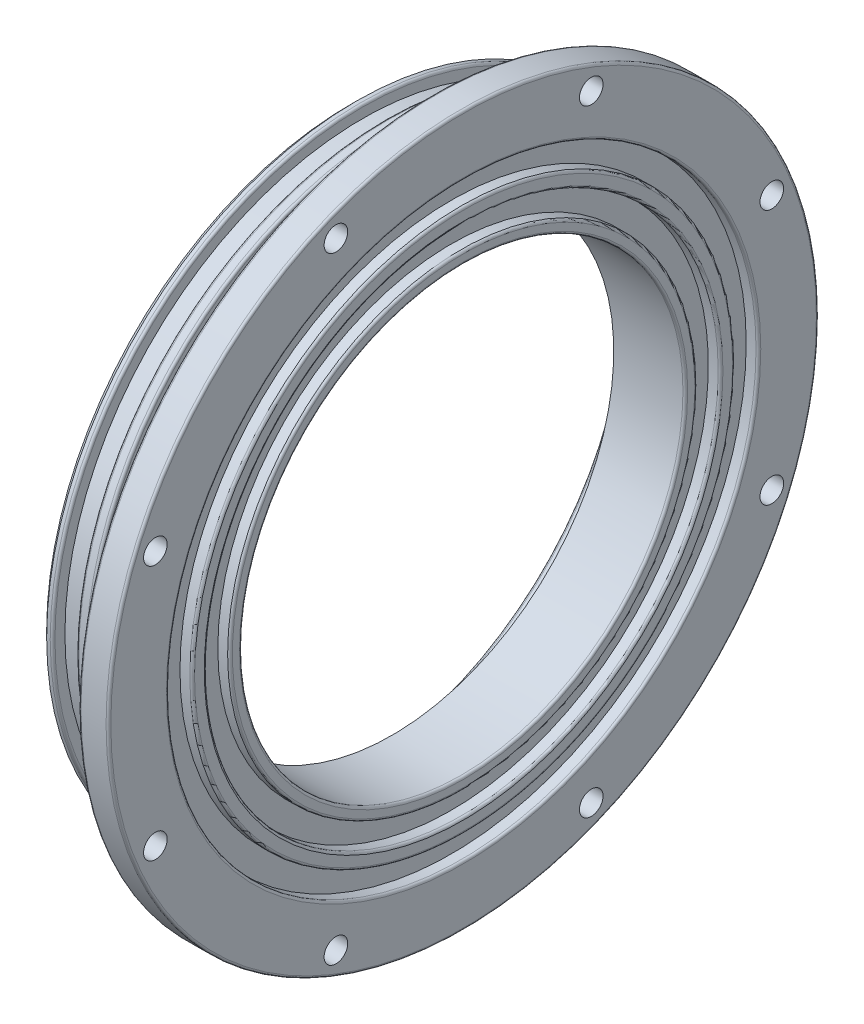
SolidWorks part; units mm, degrees
ref_plane "Front Plane" through (0, 0, 0) normal (0, 0, 1) x (1, 0, 0)
ref_plane "Top Plane" through (0, 0, 0) normal (0, 1, 0) x (1, 0, 0)
ref_plane "Right Plane" through (0, 0, 0) normal (1, 0, 0) x (0, 0, -1)
sketch "Sketch1" plane through (0, 0, 0) normal (0, 0, 1) x (1, 0, 0)
  line L0 (0, 0) -> (0, -58.42) construction
  line L5 (24.1999, -76) -> (17.8298, -76)
  line L6 (17.8298, -76) -> (17.8298, -66.421)
  line L7 (17.8298, -66.421) -> (0, -66.421) construction
  line L8 (0, -66.294) -> (0, -58.42)
  line L9 (0, -58.42) -> (8.89, -58.42)
  line L10 (0, -66.294) -> (2.54, -66.294)
  line L11 (2.54, -66.294) -> (2.54, -63.6575)
  line L12 (2.54, -63.6575) -> (7.6449, -63.6575)
  line L13 (7.6449, -63.6575) -> (7.6449, -66.294)
  line L14 (7.6449, -66.294) -> (10.1849, -66.294)
  line L15 (10.1849, -66.294) -> (10.1849, -63.6575)
  line L16 (10.1849, -63.6575) -> (15.2898, -63.6575)
  line L17 (15.2898, -63.6575) -> (15.2898, -66.294)
  line L18 (15.2898, -66.294) -> (17.8298, -66.294)
  line L19 (17.8298, -66.294) -> (17.8298, -66.421)
  line L20 (0, -66.421) -> (0, -66.294) construction
  line L24 (0, 0) -> (6.2477, 0) construction
  line L25 (8.89, -58.42) -> (8.89, -47.4495)
  line L26 (8.89, -47.4495) -> (24.1999, -47.4495)
  line L27 (24.1999, -47.4495) -> (24.1999, -49.9895)
  line L28 (24.1999, -49.9895) -> (21.59, -49.9895)
  line L29 (21.59, -49.9895) -> (21.59, -54.9896)
  line L30 (21.59, -54.9896) -> (24.1999, -54.9896)
  line L31 (24.1999, -54.9896) -> (24.1999, -58.0857)
  line L32 (24.1999, -58.0857) -> (21.59, -58.0857)
  line L33 (21.59, -58.0857) -> (21.59, -63.0858)
  line L34 (21.59, -63.0858) -> (24.1999, -63.0858)
  line L35 (24.1999, -63.0858) -> (24.1999, -76)
  dimension "CouplerIR" = 58.42
  dimension "76mm" = 76
  dimension "HullR" = 66.421
  dimension "RingSpacing" = 2.54
  dimension "GlandClearanceGap" = 0.254
  dimension "GlandWidth" = 5.1049
  dimension "D1" = 2.7635
  dimension "Planar Gland Backing Thickness" = 12.7
  dimension "OuterPlanarRingInnerRad" = 58.0857
  dimension "InnerPlanarRingInnerRad" = 49.9895
  dimension "PlanarGlandWidth" = 5.0001
  dimension "PlanarGlandDepth" = 2.6098
  dimension "D2" = 24.1999
revolve "Revolve1" add sketch "Sketch1" angle 360 about L24
chamfer "Chamfer1" distance 1.27 angle 45 1 edges at (0, 0, 66.294)
fillet "Fillet1" radius 0.508 13 edges at (8.89, 0, 58.42) (24.1999, 0, 47.4495) (24.1999, 0, 49.9895) (24.1999, 0, 54.9896) (24.1999, 0, 58.0857) (24.1999, 0, 63.0858) (24.1999, 0, 76) (17.8298, 0, 76) (15.2898, 0, 66.294) (10.1849, 0, 66.294) (7.6449, 0, 66.294) (2.54, 0, 66.294) (0, 0, 58.42)
sketch "Sketch3" plane through (24.1999, 0, 0) normal (1, 0, 0) x (0, 0, -1)
  line L1 (27.3185, -65.9527) -> (65.9527, -27.3185) construction
  line L2 (65.9527, -27.3185) -> (65.9527, 27.3185) construction
  line L3 (65.9527, 27.3185) -> (27.3185, 65.9527) construction
  line L4 (27.3185, 65.9527) -> (-27.3185, 65.9527) construction
  line L5 (-27.3185, 65.9527) -> (-65.9527, 27.3185) construction
  line L6 (-65.9527, 27.3185) -> (-65.9527, -27.3185) construction
  line L7 (-65.9527, -27.3185) -> (-27.3185, -65.9527) construction
  line L8 (-27.3185, -65.9527) -> (27.3185, -65.9527) construction
  circle A0 centre (0, 0) radius 65.9527 construction
  point P12 (-27.3185, 65.9527)
  point P13 (27.3185, 65.9527)
  point P14 (65.9527, 27.3185)
  point P15 (65.9527, -27.3185)
  point P16 (27.3185, -65.9527)
  point P17 (-27.3185, -65.9527)
  point P18 (-65.9527, -27.3185)
  point P19 (-65.9527, 27.3185)
  dimension "D1" = 142.7734
hole_wizard "#8 (0.199) Diameter Hole1" positions "Sketch3" profile "Sketch4" hole size "#8" standard "ANSI Inch"
sketch "Sketch4" plane through (24.1999, 27.3185, 65.9527) normal (0, 1, 0) x (0, 0, -1)
  line L0 (0, 0) -> (0, 10.668)
  line L1 (0, 10.668) -> (2.5273, 9.1494)
  line L2 (2.5273, 9.1494) -> (2.5273, 0)
  line L5 (2.5273, 0) -> (0, 0)
  line L10 (0, 10.668) -> (-2.5273, 9.1494) construction
  line L11 (0, -6.35) -> (0, 107.95) construction
  dimension "Hole Dia." = 5.0546
  dimension "Hole Depth" = 10.668
  dimension "Drill Angle" = 118
sketch "Sketch5" plane through (8.89, 0, 0) normal (-1, 0, 0) x (0, 0, 1)
  line L0 (-22.162, -53.5037) -> (-20.16, -48.6707) construction
  line L1 (20.16, -48.6707) -> (48.6707, -20.16) construction
  line L2 (48.6707, -20.16) -> (48.6707, 20.16) construction
  line L3 (48.6707, 20.16) -> (20.16, 48.6707) construction
  line L4 (20.16, 48.6707) -> (-20.16, 48.6707) construction
  line L5 (-20.16, 48.6707) -> (-48.6707, 20.16) construction
  line L6 (-48.6707, 20.16) -> (-48.6707, -20.16) construction
  line L7 (-48.6707, -20.16) -> (-20.16, -48.6707) construction
  line L8 (-20.16, -48.6707) -> (20.16, -48.6707) construction
  line L9 (-18.1581, -43.8376) -> (-20.16, -48.6707) construction
  line L10 (-18.1581, -43.8376) -> (-48.6707, -20.16) construction
  line L11 (20.16, -48.6707) -> (-18.1581, -43.8376) construction
  circle A0 centre (0, 0) radius 48.6707 construction
  circle A1 centre (0, 0) radius 57.912 construction
  circle A2 centre (0, 0) radius 47.4495 construction
  point P18 (-48.6707, -20.16)
  point P19 (-20.16, -48.6707)
  point P20 (20.16, -48.6707)
  point P21 (48.6707, -20.16)
  point P22 (48.6707, 20.16)
  point P23 (20.16, 48.6707)
  point P24 (-20.16, 48.6707)
  point P25 (-48.6707, 20.16)
hole_wizard "#4-40 Tapped Hole1" positions "Sketch5" profile "Sketch6" tap size "#4-40" standard "ANSI Inch"
sketch "Sketch6" plane through (8.89, 20.16, -48.6707) normal (0, 1, 0) x (0, 0, 1)
  line L0 (0, 0) -> (0, 7.62)
  line L1 (0, 7.62) -> (1.1303, 6.9408)
  line L2 (1.1303, 6.9408) -> (1.1303, 0)
  line L5 (1.1303, 0) -> (0, 0)
  line L10 (0, 7.62) -> (-1.1303, 6.9408) construction
  line L11 (0, -6.35) -> (0, 107.95) construction
  dimension "Tap Drill Dia." = 2.2606
  dimension "Tap Drill Depth" = 7.62
  dimension "Drill Angle" = 118
cosmetic thread "Hole Thread1" parameters "D1"=5.588, "D2"=2.8448
cosmetic thread "Hole Thread2" parameters "D1"=5.588, "D2"=2.8448
cosmetic thread "Hole Thread3" parameters "D1"=5.588, "D2"=2.8448
cosmetic thread "Hole Thread4" parameters "D1"=5.588, "D2"=2.8448
cosmetic thread "Hole Thread5" parameters "D1"=5.588, "D2"=2.8448
cosmetic thread "Hole Thread6" parameters "D1"=5.588, "D2"=2.8448
cosmetic thread "Hole Thread7" parameters "D1"=5.588, "D2"=2.8448
cosmetic thread "Hole Thread8" parameters "D1"=5.588, "D2"=2.8448
equation "\"HullID\"= 5.230"
equation "\"HullIR\"= \"HullID\" / 2"
equation "\"CrossSectionThickness\"= .136"
equation "\"RingCompression\"= .2"
equation "\"GlandDepth\"= \"CrossSectionThickness\" * ( 1 - \"RingCompression\" )"
equation "\"D1@Sketch1\"=\"GlandDepth\""
equation "\"HullR@Sketch1\"= \"HullIR\""
equation "\"RingCSArea\"= .0164"
equation "\"GlandFill\"= .75"
equation "\"GlandWidth\"= 1 / \"GlandFill\" * \"RingCSArea\" / \"GlandDepth\""
equation "\"GlandWidth@Sketch1\"= \"GlandWidth\""
equation "\"OuterPlanarRingNomInnerDiameter\"= 4.484"
equation "\"PlanarRingStreching\"= .02"
equation "\"PlanarRingCrosssectionDepth\"= .137"
equation "\"OuterPlanarRingInnerRad\"= \"OuterPlanarRingNomInnerDiameter\" * ( 1 + \"PlanarRingStreching\" ) / 2"
equation "\"OuterPlanarRingInnerRad@Sketch1\"= \"OuterPlanarRingInnerRad\""
equation "\"PlanarRingCommpression\"= .25"
equation "\"PlanarRingGlandDepth\"= \"PlanarRingCrosssectionDepth\" * ( 1 - \"PlanarRingCommpression\" )"
equation "\"PlanarRingCrossSectionalArea\"= .01517"
equation "\"PlanarGlandFill\"= .75"
equation "\"PlanarGlandWidth\"= \"PlanarRingCrossSectionalArea\" / \"PlanarGlandFill\" / \"PlanarRingGlandDepth\""
equation "\"PlanarGlandWidth@Sketch1\"= \"PlanarGlandWidth\""
equation "\"PlanarGlandDepth@Sketch1\"= \"PlanarRingGlandDepth\""
equation "\"InnerPlanarRingNomInnerDiameter\"= 3.859"
equation "\"InnerPlanarRingInnerRad\"= \"InnerPlanarRingNomInnerDiameter\" * ( 1 + \"PlanarRingStreching\" ) / 2"
equation "\"InnerPlanarRingInnerRad@Sketch1\"= \"InnerPlanarRingInnerRad\""
